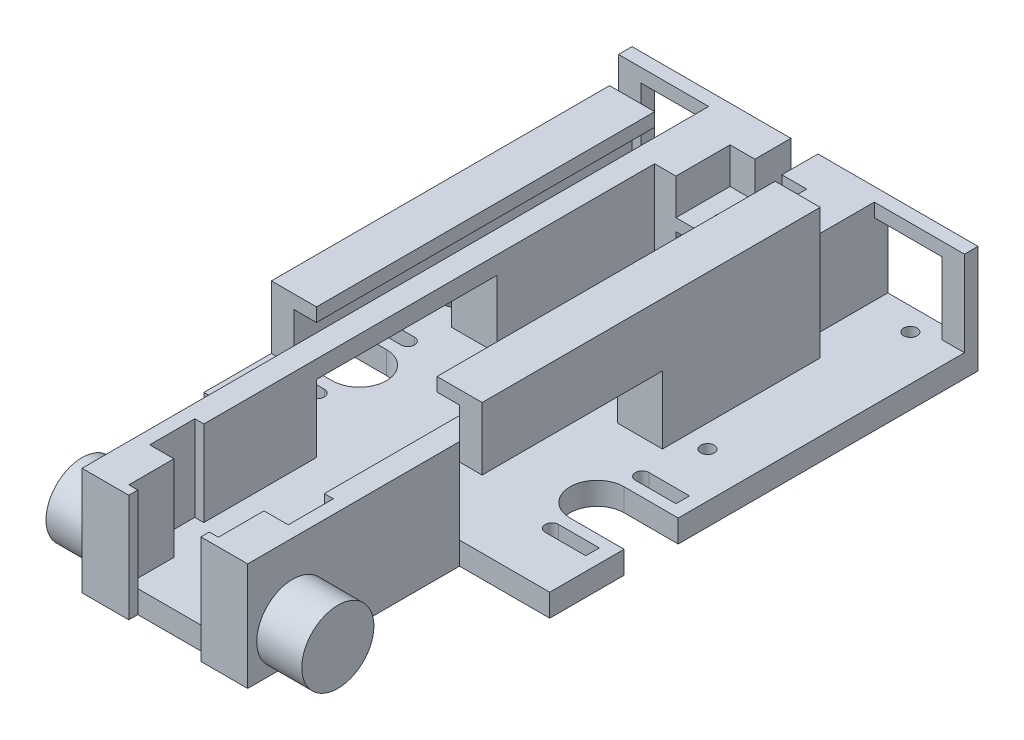
SolidWorks part; units mm, degrees
ref_plane "Front Plane" through (0, 0, 0) normal (0, 0, 1) x (1, 0, 0)
ref_plane "Top Plane" through (0, 0, 0) normal (0, 1, 0) x (1, 0, 0)
ref_plane "Right Plane" through (0, 0, 0) normal (1, 0, 0) x (0, 0, -1)
sketch "Sketch1" plane through (0, 0, 0) normal (0, 0, 1) x (1, 0, 0)
  line L0 (0, 0) -> (33.9598, 0)
  line L1 (33.9598, 0) -> (33.9598, 24.0538)
  line L2 (0, 0) -> (0, 24.0538)
  line L3 (0, 24.0538) -> (-6.35, 24.0538)
  line L4 (33.9598, 24.0538) -> (40.3098, 24.0538)
  line L5 (-6.35, 24.0538) -> (-6.35, -6.35)
  line L6 (40.3098, 24.0538) -> (40.3098, -6.35)
  line L7 (40.3098, -6.35) -> (-6.35, -6.35)
  dimension "D1" = 33.9598
  dimension "D2" = 24.0538
  dimension "D3" = 24.0538
  dimension "D4" = 6.35
  dimension "D5" = 6.35
  dimension "D6" = 8.9803
extrude "Boss-Extrude1" add sketch "Sketch1" against normal blind 203.2
sketch "Sketch3" plane through (-6.35, 0, 0) normal (-1, 0, 0) x (0, 0, 1)
  line L0 (0, 8.8519) -> (-3.81, 8.8519) construction
  line L1 (0, 24.0538) -> (0, -6.35) construction
  line L2 (-3.81, 8.8519) -> (-16.51, 8.8519) construction
  circle A0 centre (-16.51, 8.8519) radius 10.16
  dimension "D3" = 20.32
  dimension "D1" = 3.81
  dimension "D2" = 12.7
sketch "Sketch4" plane through (0, 0, 0) normal (0, 0, 1) x (1, 0, 0)
  line L1 (33.9598, 24.0538) -> (40.3098, 24.0538)
  line L2 (33.9598, 24.0538) -> (33.9598, -6.35)
  line L3 (33.9598, -6.35) -> (40.3098, -6.35)
  line L4 (40.3098, 24.0538) -> (40.3098, -6.35)
  line L5 (-6.35, -6.35) -> (0, -6.35)
  line L6 (-6.35, -6.35) -> (-6.35, 24.0538)
  line L7 (-6.35, 24.0538) -> (0, 24.0538)
  line L8 (0, -6.35) -> (0, 24.0538)
sketch "Sketch8" plane through (0, 0, -203.2) normal (0, 0, -1) x (-1, 0, 0)
  line L1 (-40.3098, -6.35) -> (-33.9598, -6.35)
  line L2 (-40.3098, -6.35) -> (-40.3098, 24.0538)
  line L3 (-40.3098, 24.0538) -> (-33.9598, 24.0538)
  line L4 (-33.9598, -6.35) -> (-33.9598, 24.0538)
  line L5 (6.35, -6.35) -> (0, -6.35)
  line L6 (6.35, -6.35) -> (6.35, 24.0538)
  line L7 (6.35, 24.0538) -> (0, 24.0538)
  line L8 (0, -6.35) -> (0, 24.0538)
extrude "Boss-Extrude9" add sketch "Sketch8" along normal blind 6.35
sketch "Sketch9" plane through (0, 0, 0) normal (1, 0, 0) x (0, 0, -1)
  line L1 (203.2, -6.35) -> (209.55, -6.35)
  line L2 (203.2, -6.35) -> (203.2, 24.0538)
  line L3 (203.2, 24.0538) -> (209.55, 24.0538)
  line L4 (209.55, -6.35) -> (209.55, 24.0538)
extrude "Boss-Extrude10" add sketch "Sketch9" along normal up to next
extrude "Boss-Extrude11" add sketch "Sketch4" along normal blind 6.35
sketch "Sketch10" plane through (33.9598, 0, 0) normal (-1, 0, 0) x (0, 0, 1)
  line L1 (0, -6.35) -> (6.35, -6.35)
  line L2 (0, -6.35) -> (0, 24.0538)
  line L3 (0, 24.0538) -> (6.35, 24.0538)
  line L4 (6.35, -6.35) -> (6.35, 24.0538)
extrude "Boss-Extrude12" add sketch "Sketch10" along normal up to next
sketch "Sketch13" plane through (40.3098, 0, 0) normal (1, 0, 0) x (0, 0, -1)
  line L0 (-6.35, 8.8519) -> (50.8, 8.8519) construction
  line L1 (-6.35, -6.35) -> (-6.35, 24.0538) construction
  line L2 (50.8, -6.35) -> (50.8, 0)
  line L3 (209.55, -6.35) -> (-6.35, -6.35) construction
  line L5 (50.8, 0) -> (101.6, 0)
  line L6 (50.8, 0) -> (50.8, 19.05)
  line L7 (50.8, 19.05) -> (101.6, 19.05)
  line L8 (101.6, 0) -> (101.6, 19.05)
  line L9 (50.8, 0) -> (101.6, 0)
  line L10 (50.8, 0) -> (50.8, -6.35)
  line L11 (50.8, -6.35) -> (101.6, -6.35)
  line L12 (101.6, 0) -> (101.6, -6.35)
  dimension "D1" = 57.15
  dimension "D2" = 6.35
  dimension "D3" = 19.05
  dimension "D4" = 50.8
extrude "Cut-Extrude3" cut sketch "Sketch13" against normal through all contours L5 L8 L7 L6
sketch "Sketch14" plane through (40.3098, 0, 0) normal (1, 0, 0) x (0, 0, -1)
  line L0 (209.55, -6.35) -> (-6.35, -6.35) construction
  line L1 (50.8, 0) -> (95.25, 0)
  line L2 (50.8, 0) -> (50.8, -6.35)
  line L3 (50.8, -6.35) -> (95.25, -6.35)
  line L4 (95.25, 0) -> (95.25, -6.35)
extrude "Boss-Extrude13" add sketch "Sketch14" along normal blind 25.4
sketch "Sketch15" plane through (-6.35, 0, 0) normal (-1, 0, 0) x (0, 0, 1)
  line L0 (-50.8, 0) -> (-50.8, -6.35)
  line L1 (-209.55, -6.35) -> (6.35, -6.35) construction
  line L3 (-101.6, 0) -> (-50.8, 0)
  line L4 (-101.6, 0) -> (-101.6, -6.35)
  line L5 (-101.6, -6.35) -> (-50.8, -6.35)
  line L6 (-50.8, 0) -> (-50.8, -6.35)
  line M2 (-50.8, 0) -> (-101.6, 0)
  line M7 (-209.55, -6.35) -> (6.35, -6.35)
extrude "Boss-Extrude14" add sketch "Sketch15" along normal blind 25.4 contours L4 L0 M2 M7
sketch "Sketch18" plane through (0, 0, 0) normal (0, 1, 0) x (1, 0, 0)
  line L0 (16.9799, 203.2) -> (16.9799, 0) construction
  line L1 (33.9598, 203.2) -> (0, 203.2) construction
  line L2 (33.9598, 0) -> (0, 0) construction
  line L3 (65.7098, 73.025) -> (25.4, 73.025) construction
  line L4 (65.7098, 95.25) -> (65.7098, 50.8) construction
  line L5 (25.4, 73.025) -> (44.45, 73.025)
  circle A0 centre (44.45, 73.025) radius 6.35
  circle A1 centre (-10.4902, 73.025) radius 6.35
  dimension "D1" = 12.7
sketch "Sketch20" plane through (0, 0, -209.55) normal (0, 0, -1) x (-1, 0, 0)
  line L0 (-40.3098, 24.0538) -> (-40.3098, -6.35) construction
  line L1 (6.35, 24.0538) -> (-40.3098, 24.0538)
  line L2 (6.35, 24.0538) -> (6.35, 13.8938)
  line L3 (6.35, 13.8938) -> (-40.3098, 13.8938)
  line L4 (-40.3098, 24.0538) -> (-40.3098, 13.8938)
  dimension "D1" = 10.16
extrude "Cut-Extrude6" cut sketch "Sketch20" against normal blind 6.35
sketch "Sketch28" plane through (0, 0, -95.25) normal (0, 0, -1) x (-1, 0, 0)
  line L1 (-40.3098, 0) -> (-65.7098, 0)
  line L2 (-40.3098, 0) -> (-40.3098, -6.35)
  line L3 (-40.3098, -6.35) -> (-65.7098, -6.35)
  line L4 (-65.7098, 0) -> (-65.7098, -6.35)
extrude "Boss-Extrude16" add sketch "Sketch28" along normal blind 6.35
sketch "Sketch29" plane through (0, 0, 0) normal (0, 1, 0) x (1, 0, 0)
  line L2 (65.7098, 101.6) -> (50.4698, 101.6)
  line L3 (50.4698, 101.6) -> (50.4698, 79.375)
  line L4 (16.9799, 0) -> (16.9799, 203.2) construction
  line L5 (50.4698, 101.6) -> (65.7098, 101.6)
  circle A0 centre (50.4698, 79.375) radius 7.62
  circle A1 centre (-16.51, 79.375) radius 7.62
  dimension "D2" = 15.24
  dimension "D1" = 22.225
extrude "Cut-Extrude7" cut sketch "Sketch29" against normal up to surface (6.35 mm away) up to face at (16.9799, -6.35, -84.6667)
sketch "Sketch30" plane through (0, 0, 0) normal (0, 1, 0) x (1, 0, 0)
  line L0 (50.4698, 86.995) -> (65.7098, 86.995)
  line L1 (65.7098, 101.6) -> (65.7098, 50.8) construction
  line L2 (65.7098, 86.995) -> (65.7098, 71.755)
  line L3 (65.7098, 71.755) -> (50.4698, 71.755)
  line L4 (16.9799, 203.2) -> (16.9799, 0) construction
  line L5 (-31.75, 86.995) -> (-31.75, 71.755)
  line L6 (-31.75, 71.755) -> (-16.51, 71.755)
  line L7 (-16.51, 86.995) -> (-31.75, 86.995)
  circle A0 centre (50.4698, 79.375) radius 7.62 construction
  arc A1 (50.4698, 86.995) -> (50.4698, 71.755) centre (50.4698, 79.375) cw
  arc A2 (-16.51, 86.995) -> (-16.51, 71.755) centre (-16.51, 79.375) ccw
extrude "Cut-Extrude8" cut sketch "Sketch30" against normal blind 6.35
sketch "Sketch32" plane through (40.3098, 0, 0) normal (1, 0, 0) x (0, 0, -1)
  line L0 (-6.35, -6.35) -> (-6.35, 3.81) construction
  line L1 (-6.35, -6.35) -> (-6.35, 24.0538) construction
  line L2 (-6.35, 3.81) -> (3.81, 3.81) construction
  circle A0 centre (3.81, 3.81) radius 10.16
  dimension "D3" = 20.32
  dimension "D1" = 10.16
  dimension "D2" = 10.16
extrude "Boss-Extrude17" add sketch "Sketch32" along normal blind 12.7
sketch "Sketch33" plane through (-6.35, 0, 0) normal (-1, 0, 0) x (0, 0, 1)
  line L0 (6.35, -6.35) -> (6.35, 3.81)
  line L1 (6.35, 24.0538) -> (6.35, -6.35) construction
  line L2 (6.35, 3.81) -> (-3.81, 3.81)
  circle A0 centre (-3.81, 3.81) radius 10.16
  dimension "D1" = 10.16
  dimension "D2" = 10.16
extrude "Boss-Extrude18" add sketch "Sketch33" along normal blind 12.7
sketch "Sketch34" plane through (0, 0, -209.55) normal (0, 0, -1) x (-1, 0, 0)
  line L1 (-40.3098, -6.35) -> (10.9504, -6.35)
  line L2 (-40.3098, -6.35) -> (-40.3098, 38.0137)
  line L3 (-40.3098, 38.0137) -> (10.9504, 38.0137)
  line L4 (10.9504, -6.35) -> (10.9504, 38.0137)
extrude "Cut-Extrude9" cut sketch "Sketch34" against normal blind 63.5
sketch "Sketch35" plane through (0, 0, -146.05) normal (0, 0, -1) x (-1, 0, 0)
  line L1 (-40.3098, -6.35) -> (6.35, -6.35)
  line L2 (-40.3098, -6.35) -> (-40.3098, 24.0538)
  line L3 (-40.3098, 24.0538) -> (6.35, 24.0538)
  line L4 (6.35, -6.35) -> (6.35, 24.0538)
extrude "Boss-Extrude19" add sketch "Sketch35" along normal blind 6.35
sketch "Sketch36" plane through (0, 0, -152.4) normal (0, 0, -1) x (-1, 0, 0)
  line L0 (-40.3098, -6.35) -> (-27.6098, -6.35)
  line L1 (-40.3098, -6.35) -> (6.35, -6.35) construction
  line L2 (-27.6098, -6.35) -> (-27.6098, 0)
  line L3 (6.35, 24.0538) -> (-40.3098, 24.0538) construction
  line L8 (-27.6098, 24.0538) -> (-6.0198, 24.0538)
  line L9 (-27.6098, 24.0538) -> (-27.6098, 13.8938)
  line L10 (-27.6098, 13.8938) -> (-6.0198, 13.8938)
  line L11 (-6.0198, 24.0538) -> (-6.0198, 13.8938)
  dimension "D1" = 10.16
  dimension "D3" = 12.7
  dimension "D4" = 21.59
extrude "Cut-Extrude10" cut sketch "Sketch36" against normal blind 6.35 contours L9 L8 L11 L10
sketch "Sketch37" plane through (0, 0, -101.6) normal (0, 0, -1) x (-1, 0, 0)
  line L1 (-65.7098, 0) -> (-40.3098, 0)
  line L2 (-65.7098, 0) -> (-65.7098, -6.35)
  line L3 (-65.7098, -6.35) -> (-40.3098, -6.35)
  line L4 (-40.3098, 0) -> (-40.3098, -6.35)
  line L5 (6.35, 0) -> (31.75, 0)
  line L6 (6.35, 0) -> (6.35, -6.35)
  line L7 (6.35, -6.35) -> (31.75, -6.35)
  line L8 (31.75, 0) -> (31.75, -6.35)
extrude "Boss-Extrude20" add sketch "Sketch37" along normal blind 12.7
sketch "Sketch38" plane through (0, -6.35, 0) normal (0, -1, 0) x (1, 0, 0)
  line L0 (16.9799, -152.4) -> (16.9799, 6.35) construction
  line L1 (40.3098, -152.4) -> (-6.35, -152.4) construction
  line L2 (-6.35, 6.35) -> (40.3098, 6.35) construction
  line L3 (53.0098, -114.3) -> (53.0098, -107.95) construction
  line L4 (65.7098, -114.3) -> (40.3098, -114.3) construction
  circle A0 centre (53.0098, -107.95) radius 1.905
  circle A1 centre (-19.05, -107.95) radius 1.905
  dimension "D2" = 3.81
  dimension "D1" = 6.35
extrude "Cut-Extrude11" cut sketch "Sketch38" against normal blind 12.7
sketch "Sketch39" plane through (0, 0, 0) normal (0, 1, 0) x (1, 0, 0)
  line L0 (50.4698, 86.995) -> (50.4698, 92.075)
  line L1 (50.4698, 71.755) -> (50.4698, 66.675)
  line L2 (50.4698, 68.58) -> (61.8998, 68.58)
  line L3 (50.4698, 64.77) -> (61.8998, 64.77)
  line L4 (61.8998, 64.77) -> (61.8998, 68.58)
  line L5 (50.4698, 93.98) -> (61.8998, 93.98)
  line L6 (50.4698, 90.17) -> (61.8998, 90.17)
  line L7 (61.8998, 90.17) -> (61.8998, 93.98)
  line L8 (17.4498, 152.4) -> (17.4498, 7.6403) construction
  line L9 (27.6098, 152.4) -> (7.2898, 152.4) construction
  line L10 (-27.0002, 90.17) -> (-27.0002, 93.98)
  line L11 (-15.5702, 90.17) -> (-27.0002, 90.17)
  line L12 (-15.5702, 93.98) -> (-27.0002, 93.98)
  line L13 (-15.5702, 68.58) -> (-27.0002, 68.58)
  line L14 (-27.0002, 64.77) -> (-27.0002, 68.58)
  line L15 (-15.5702, 64.77) -> (-27.0002, 64.77)
  circle A0 centre (50.4698, 92.075) radius 1.905
  circle A1 centre (50.4698, 66.675) radius 1.905
  circle A2 centre (-15.5702, 92.075) radius 1.905
  circle A3 centre (-15.5702, 66.675) radius 1.905
  dimension "D3" = 11.43
  dimension "D1" = 5.08
  dimension "D2" = 5.08
sketch "Sketch44" plane through (0, 13.8938, 0) normal (0, 1, 0) x (1, 0, 0)
  line L0 (16.8148, 146.05) -> (12.0523, 146.05) construction
  line L1 (27.6098, 146.05) -> (6.0198, 146.05) construction
  line L2 (16.8148, 146.05) -> (21.5773, 146.05) construction
  line L3 (21.5773, 152.4) -> (21.5773, 149.225)
  line L4 (27.6098, 152.4) -> (6.0198, 152.4) construction
  line L5 (12.0523, 152.4) -> (12.0523, 149.225)
  circle A0 centre (21.5773, 149.225) radius 1.143
  circle A1 centre (12.0523, 149.225) radius 1.143
  dimension "D4" = 2.286
  dimension "D5" = 2.286
  dimension "D1" = 4.7625
  dimension "D2" = 3.175
  dimension "D3" = 3.175
  dimension "D6" = 9.525
extrude "Cut-Extrude15" cut sketch "Sketch44" against normal through all both and the other way through all
extrude "Cut-Extrude13" cut sketch "Sketch39" against normal blind 8.35
sketch "Sketch40" plane through (0, 24.0538, 0) normal (0, 1, 0) x (1, 0, 0)
  line L0 (16.9799, -6.35) -> (29.6799, -6.35)
  line L1 (40.3098, -6.35) -> (-6.35, -6.35) construction
  line L2 (16.9799, -6.35) -> (4.2799, -6.35)
  line L3 (0, 0) -> (33.9598, 0) construction
  line L4 (4.2799, -6.35) -> (29.6799, -6.35)
  line L5 (4.2799, -6.35) -> (4.2799, 0)
  line L6 (4.2799, 0) -> (29.6799, 0)
  line L7 (29.6799, -6.35) -> (29.6799, 0)
  line M4 (33.9598, 0) -> (0, 0)
  line M7 (-6.35, -6.35) -> (40.3098, -6.35)
extrude "Cut-Extrude14" cut sketch "Sketch40" against normal up to surface (24.0538 mm away) contours L7 L5 M7 M4
sketch "Sketch47" plane through (0, -6.35, 0) normal (0, -1, 0) x (-1, 0, 0)
  line L0 (-16.9799, 152.4) -> (-16.9799, 142.24) construction
  line L1 (-40.3098, 152.4) -> (6.35, 152.4) construction
  circle A0 centre (-16.9799, 142.24) radius 3.556
extrude "Cut-Extrude16" cut sketch "Sketch47" against normal through all
sketch "Sketch48" plane through (0, 13.8938, 0) normal (0, 1, 0) x (1, 0, 0)
  line L0 (21.5773, 148.082) -> (21.5773, 146.05) construction
  line L1 (27.6098, 146.05) -> (6.0198, 146.05) construction
  line L2 (12.0523, 148.082) -> (12.0523, 146.05) construction
  line L3 (21.5773, 146.05) -> (12.0523, 146.05)
  circle A0 centre (21.5773, 149.225) radius 1.143 construction
  circle A1 centre (12.0523, 149.225) radius 1.143 construction
  arc A2 (21.5773, 146.05) -> (12.0523, 146.05) centre (16.8148, 141.2875) ccw
extrude "Cut-Extrude17" cut sketch "Sketch48" against normal up to surface (13.8938 mm away) contours L3 A2 up to face at (16.9799, 0, -138.684)
sketch "Sketch49" plane through (-6.35, 0, 0) normal (-1, 0, 0) x (0, 0, 1)
  line L1 (-152.4, 24.0538) -> (-50.8, 24.0538)
  line L2 (-152.4, 24.0538) -> (-152.4, 19.05)
  line L3 (-152.4, 19.05) -> (-50.8, 19.05)
  line L4 (-50.8, 24.0538) -> (-50.8, 19.05)
extrude "Boss-Extrude23" add sketch "Sketch49" along normal blind 6.35
sketch "Sketch50" plane through (40.3098, 0, 0) normal (1, 0, 0) x (0, 0, -1)
  line L1 (152.4, 24.0538) -> (50.8, 24.0538)
  line L2 (152.4, 24.0538) -> (152.4, 19.05)
  line L3 (152.4, 19.05) -> (50.8, 19.05)
  line L4 (50.8, 24.0538) -> (50.8, 19.05)
extrude "Boss-Extrude24" add sketch "Sketch50" along normal blind 6.35
sketch "Sketch51" plane through (0, 0, 0) normal (0, 1, 0) x (1, 0, 0)
  circle A0 centre (16.9799, 142.24) radius 3.556
  circle A1 centre (16.9799, 142.24) radius 4.7625
extrude "Cut-Extrude18" cut sketch "Sketch51" against normal blind 3.556
sketch "Sketch52" plane through (0, 24.0538, 0) normal (0, 1, 0) x (1, 0, 0)
  line L0 (-12.7, 152.4) -> (6.0198, 152.4) construction
  line L1 (-12.7, 50.8) -> (-6.35, 50.8)
  line L2 (-12.7, 50.8) -> (-12.7, 152.4)
  line L3 (-12.7, 152.4) -> (-6.35, 152.4)
  line L4 (-6.35, 50.8) -> (-6.35, 152.4)
  line L5 (27.6098, 152.4) -> (46.6598, 152.4) construction
  line L6 (46.6598, 50.8) -> (37.1348, 50.8)
  line L7 (46.6598, 50.8) -> (46.6598, 152.4)
  line L8 (46.6598, 152.4) -> (37.1348, 152.4)
  line L9 (37.1348, 50.8) -> (37.1348, 152.4)
extrude "Boss-Extrude25" add sketch "Sketch52" along normal blind 15.24
sketch "Sketch53" plane through (0, 39.2938, 0) normal (0, 1, 0) x (1, 0, 0)
  line L0 (-12.7, 152.4) -> (-12.7, 50.8) construction
  line L1 (46.6598, 50.8) -> (-12.7, 50.8)
  line L2 (46.6598, 50.8) -> (46.6598, 133.35)
  line L3 (46.6598, 133.35) -> (-12.7, 133.35)
  line L4 (-12.7, 50.8) -> (-12.7, 133.35)
  dimension "D1" = 82.55
extrude "Boss-Extrude26" add sketch "Sketch53" along normal blind 3.175
sketch "Sketch54" plane through (0, 0, -152.4) normal (0, 0, -1) x (-1, 0, 0)
  line L1 (12.7, 39.2938) -> (6.35, 39.2938)
  line L2 (12.7, 39.2938) -> (12.7, 19.05)
  line L3 (12.7, 19.05) -> (6.35, 19.05)
  line L4 (6.35, 39.2938) -> (6.35, 19.05)
  line L5 (-40.3098, 19.05) -> (-46.6598, 19.05)
  line L6 (-40.3098, 19.05) -> (-40.3098, 39.2938)
  line L7 (-40.3098, 39.2938) -> (-46.6598, 39.2938)
  line L8 (-46.6598, 19.05) -> (-46.6598, 39.2938)
extrude "Cut-Extrude20" cut sketch "Sketch54" against normal up to surface (19.05 mm away) up to face at (16.4507, 40.3521, -133.35)
sketch "Sketch55" plane through (0, 0, -152.4) normal (0, 0, -1) x (-1, 0, 0)
  line L1 (-40.3098, 39.2938) -> (-37.1348, 39.2938)
  line L2 (-40.3098, 39.2938) -> (-40.3098, 24.0538)
  line L3 (-40.3098, 24.0538) -> (-37.1348, 24.0538)
  line L4 (-37.1348, 39.2938) -> (-37.1348, 24.0538)
extrude "Cut-Extrude21" cut sketch "Sketch55" against normal up to surface (101.6 mm away) up to face at (-3.175, 9.525, -50.8)
sketch "Sketch56" plane through (0, 0, -152.4) normal (0, 0, -1) x (-1, 0, 0)
  line L0 (-16.9799, -6.35) -> (-16.9799, 8.89)
  line L1 (-40.3098, -6.35) -> (6.35, -6.35) construction
  line L2 (-6.0198, 13.8938) -> (-6.0198, 8.89)
  line L3 (-27.6098, 13.8938) -> (-27.6098, 8.89)
  line L5 (-27.6098, 8.89) -> (-6.0198, 8.89)
  line L6 (-27.6098, 8.89) -> (-27.6098, 10.49)
  line L7 (-27.6098, 10.49) -> (-6.0198, 10.49)
  line L8 (-6.0198, 8.89) -> (-6.0198, 10.49)
  dimension "D1" = 1.6
  dimension "D2" = 15.24
extrude "Cut-Extrude23" cut sketch "Sketch56" against normal up to surface (6.35 mm away) contours L7 L3 L5 L2 up to face at (27.7156, 12.6492, -146.05)
sketch "Sketch57" plane through (0, 0, -133.35) normal (0, 0, -1) x (-1, 0, 0)
  line L0 (6.35, 19.05) -> (12.7, 19.05)
  line L1 (12.7, 19.05) -> (12.7, 42.4688)
  line L2 (12.7, 42.4688) -> (-46.6598, 42.4688)
  line L3 (-46.6598, 42.4688) -> (-46.6598, 19.05)
  line L4 (-46.6598, 19.05) -> (-40.3098, 19.05)
  line L5 (-40.3098, 19.05) -> (-40.3098, 39.2938)
  line L6 (-40.3098, 39.2938) -> (6.35, 39.2938)
  line L7 (6.35, 39.2938) -> (6.35, 19.05)
extrude "Cut-Extrude25" cut sketch "Sketch57" against normal up to surface (19.05 mm away) up to face at (-19.05, -3.175, -114.3)
sketch "Sketch58" plane through (0, 0, 6.35) normal (0, 0, 1) x (1, 0, 0)
  line L0 (-6.35, -6.35) -> (40.3098, -6.35) construction
  line L1 (29.6799, 24.0538) -> (32.2199, 24.0538)
  line L2 (29.6799, 24.0538) -> (29.6799, -6.35)
  line L3 (29.6799, -6.35) -> (32.2199, -6.35)
  line L4 (32.2199, 24.0538) -> (32.2199, -6.35)
  line L6 (4.2799, 24.0538) -> (1.7399, 24.0538)
  line L7 (4.2799, 24.0538) -> (4.2799, -6.35)
  line L8 (4.2799, -6.35) -> (1.7399, -6.35)
  line L9 (1.7399, 24.0538) -> (1.7399, -6.35)
  dimension "D1" = 2.54
  dimension "D2" = 2.54
extrude "Boss-Extrude27" add sketch "Sketch58" along normal blind 2.54
sketch "Sketch59" plane through (4.2799, 0, 0) normal (1, 0, 0) x (0, 0, -1)
  line L1 (-8.89, 24.0538) -> (-6.35, 24.0538)
  line L2 (-8.89, 24.0538) -> (-8.89, -6.35)
  line L3 (-8.89, -6.35) -> (-6.35, -6.35)
  line L4 (-6.35, 24.0538) -> (-6.35, -6.35)
extrude "Boss-Extrude28" add sketch "Sketch59" along normal blind 2.54
sketch "Sketch60" plane through (29.6799, 0, 0) normal (-1, 0, 0) x (0, 0, 1)
  line L0 (8.89, -6.35) -> (6.35, -6.35) construction
  line L1 (8.89, 24.0538) -> (6.5199, 24.0538)
  line L2 (8.89, 24.0538) -> (8.89, -6.35)
  line L3 (8.89, -6.35) -> (6.5199, -6.35)
  line L4 (6.5199, 24.0538) -> (6.5199, -6.35)
extrude "Boss-Extrude29" add sketch "Sketch60" along normal blind 2.54
sketch "Sketch61" plane through (1.7399, 0, 0) normal (-1, 0, 0) x (0, 0, 1)
  line L1 (6.35, -6.35) -> (8.89, -6.35)
  line L2 (6.35, -6.35) -> (6.35, 24.0538)
  line L3 (6.35, 24.0538) -> (8.89, 24.0538)
  line L4 (8.89, -6.35) -> (8.89, 24.0538)
extrude "Boss-Extrude30" add sketch "Sketch61" along normal up to surface (8.0899 mm away) up to face at (-6.35, -3.6647, 3.6647)
sketch "Sketch62" plane through (32.2199, 0, 0) normal (1, 0, 0) x (0, 0, -1)
  line L1 (-6.35, 24.0538) -> (-8.89, 24.0538)
  line L2 (-6.35, 24.0538) -> (-6.35, -6.35)
  line L3 (-6.35, -6.35) -> (-8.89, -6.35)
  line L4 (-8.89, 24.0538) -> (-8.89, -6.35)
extrude "Boss-Extrude31" add sketch "Sketch62" along normal up to surface (8.0899 mm away) up to face at (40.3098, 31.6738, -82.55)
sketch "Sketch63" plane through (0, 0, 0) normal (0, 0, -1) x (-1, 0, 0)
  line L1 (0, 0) -> (-4.2799, 0)
  line L2 (0, 0) -> (0, 24.0538)
  line L3 (0, 24.0538) -> (-4.2799, 24.0538)
  line L4 (-4.2799, 0) -> (-4.2799, 24.0538)
  line L5 (-33.9598, 0) -> (-29.6799, 0)
  line L6 (-33.9598, 0) -> (-33.9598, 24.0538)
  line L7 (-33.9598, 24.0538) -> (-29.6799, 24.0538)
  line L8 (-29.6799, 0) -> (-29.6799, 24.0538)
extrude "Boss-Extrude32" add sketch "Sketch63" along normal blind 6.35
sketch "Sketch64" plane through (0, 24.0538, 0) normal (0, 1, 0) x (1, 0, 0)
  line L1 (0, 6.35) -> (-2.54, 6.35)
  line L2 (0, 6.35) -> (0, 19.05)
  line L3 (0, 19.05) -> (-2.54, 19.05)
  line L4 (-2.54, 6.35) -> (-2.54, 19.05)
  line L5 (33.9598, 6.35) -> (36.4998, 6.35)
  line L6 (33.9598, 6.35) -> (33.9598, 19.05)
  line L7 (33.9598, 19.05) -> (36.4998, 19.05)
  line L8 (36.4998, 6.35) -> (36.4998, 19.05)
  dimension "D1" = 2.54
  dimension "D2" = 12.7
  dimension "D3" = 2.54
  dimension "D4" = 12.7
extrude "Cut-Extrude26" cut sketch "Sketch64" against normal up to surface (24.0538 mm away) up to face at (16.9799, 0, -137.4775)
sketch "Sketch65" plane through (0, 0, -152.4) normal (0, 0, -1) x (-1, 0, 0)
  line L0 (6.35, 24.0538) -> (-6.0198, 24.0538)
  line L1 (-6.0198, 24.0538) -> (-6.0198, 13.8938)
  line L2 (-6.0198, 13.8938) -> (-27.6098, 13.8938)
  line L3 (-27.6098, 13.8938) -> (-27.6098, 24.0538)
  line L4 (-27.6098, 24.0538) -> (-40.3098, 24.0538)
  line L5 (-40.3098, 24.0538) -> (-40.3098, -6.35)
  line L6 (-40.3098, -6.35) -> (6.35, -6.35)
  line L7 (6.35, -6.35) -> (6.35, 24.0538)
extrude "Boss-Extrude34" add sketch "Sketch65" along normal blind 19.05
sketch "Sketch66" plane through (0, 42.4688, 0) normal (0, 1, 0) x (1, 0, 0)
  line L1 (46.6598, 50.8) -> (-12.7, 50.8)
  line L2 (46.6598, 50.8) -> (46.6598, 114.3)
  line L3 (46.6598, 114.3) -> (-12.7, 114.3)
  line L4 (-12.7, 50.8) -> (-12.7, 114.3)
extrude "Cut-Extrude27" cut sketch "Sketch66" against normal up to surface (18.415 mm away) up to face at (33.6441, 24.0538, -58.5772)
sketch "Sketch67" plane through (0, 19.05, 0) normal (0, -1, 0) x (1, 0, 0)
  line L1 (40.3098, -101.6) -> (46.6598, -101.6)
  line L2 (40.3098, -101.6) -> (40.3098, -114.3)
  line L3 (40.3098, -114.3) -> (46.6598, -114.3)
  line L4 (46.6598, -101.6) -> (46.6598, -114.3)
extrude "Boss-Extrude35" add sketch "Sketch67" along normal blind 19.05
sketch "Sketch68" plane through (0, 19.05, 0) normal (0, -1, 0) x (1, 0, 0)
  line L1 (-6.35, -101.6) -> (-12.7, -101.6)
  line L2 (-6.35, -101.6) -> (-6.35, -114.3)
  line L3 (-6.35, -114.3) -> (-12.7, -114.3)
  line L4 (-12.7, -101.6) -> (-12.7, -114.3)
extrude "Boss-Extrude36" add sketch "Sketch68" along normal blind 19.05
sketch "Sketch69" plane through (0, 24.0538, 0) normal (0, 1, 0) x (1, 0, 0)
  line L1 (40.3098, 50.8) -> (46.6598, 50.8)
  line L2 (40.3098, 50.8) -> (40.3098, 114.3)
  line L3 (40.3098, 114.3) -> (46.6598, 114.3)
  line L4 (46.6598, 50.8) -> (46.6598, 114.3)
  line L5 (-6.35, 50.8) -> (-12.7, 50.8)
  line L6 (-6.35, 50.8) -> (-6.35, 114.3)
  line L7 (-6.35, 114.3) -> (-12.7, 114.3)
  line L8 (-12.7, 50.8) -> (-12.7, 114.3)
extrude "Boss-Extrude39" add sketch "Sketch69" along normal blind 12.7
sketch "Sketch70" plane through (40.3098, 0, 0) normal (-1, 0, 0) x (0, 0, 1)
  line L0 (-114.3, 36.7538) -> (-114.3, 24.0538) construction
  line L1 (-50.8, 36.7538) -> (-114.3, 36.7538)
  line L2 (-50.8, 36.7538) -> (-50.8, 32.9438)
  line L3 (-50.8, 32.9438) -> (-114.3, 32.9438)
  line L4 (-114.3, 36.7538) -> (-114.3, 32.9438)
  dimension "D1" = 3.81
extrude "Boss-Extrude40" add sketch "Sketch70" along normal up to surface (6.35 mm away) up to face at (33.9598, 10.7759, -79.375)
sketch "Sketch71" plane through (-6.35, 0, 0) normal (1, 0, 0) x (0, 0, -1)
  line L1 (50.8, 36.7538) -> (114.3, 36.7538)
  line L2 (50.8, 36.7538) -> (50.8, 32.9438)
  line L3 (50.8, 32.9438) -> (114.3, 32.9438)
  line L4 (114.3, 36.7538) -> (114.3, 32.9438)
  dimension "D1" = 3.81
extrude "Boss-Extrude41" add sketch "Sketch71" along normal up to surface (6.35 mm away) up to face at (0, 10.7759, -79.375)
sketch "Sketch72" plane through (0, 13.8938, 0) normal (0, 1, 0) x (1, 0, 0)
  line L0 (12.0523, 152.3236) -> (12.0523, 146.05)
  line L1 (21.5773, 146.05) -> (21.5773, 152.3236)
  circle A0 centre (12.0523, 152.3236) radius 1.0865
  circle A1 centre (21.5773, 152.3236) radius 1.143
extrude "Cut-Extrude29" cut sketch "Sketch72" against normal through all
sketch "Sketch73" plane through (0, 13.8938, 0) normal (0, 1, 0) x (1, 0, 0)
  circle A0 centre (12.0523, 149.225) radius 1.143
  circle A1 centre (21.5773, 149.225) radius 1.143
extrude "Boss-Extrude42" add sketch "Sketch73" against normal up to surface (20.2438 mm away) up to face at (12.0523, -6.35, -151.2371)
sketch "Sketch74" plane through (0, 0, -146.05) normal (0, 0, 1) x (1, 0, 0)
  line L1 (6.0198, 10.49) -> (27.6098, 10.49)
  line L2 (6.0198, 10.49) -> (6.0198, 8.89)
  line L3 (6.0198, 8.89) -> (27.6098, 8.89)
  line L4 (27.6098, 10.49) -> (27.6098, 8.89)
extrude "Cut-Extrude30" cut sketch "Sketch74" against normal blind 10.16
sketch "Sketch75" plane through (0, 0, -171.45) normal (0, 0, -1) x (-1, 0, 0)
  line L1 (6.35, 24.0538) -> (-40.3098, 24.0538)
  line L2 (6.35, 24.0538) -> (6.35, -6.35)
  line L3 (6.35, -6.35) -> (-40.3098, -6.35)
  line L4 (-40.3098, 24.0538) -> (-40.3098, -6.35)
extrude "Boss-Extrude43" add sketch "Sketch75" against normal blind 10.16
sketch "Sketch76" plane through (0, 24.0538, 0) normal (0, 1, 0) x (1, 0, 0)
  line L0 (16.8148, 161.29) -> (20.6248, 161.29)
  line L1 (6.0198, 161.29) -> (27.6098, 161.29) construction
  line L2 (20.6248, 161.29) -> (20.6248, 171.45)
  line L3 (-6.35, 171.45) -> (40.3098, 171.45) construction
  line L4 (20.6248, 171.45) -> (13.0048, 171.45)
  line L5 (13.0048, 171.45) -> (13.0048, 161.29)
  line L6 (13.0048, 161.29) -> (16.8148, 161.29)
  dimension "D1" = 3.81
  dimension "D2" = 3.81
extrude "Cut-Extrude32" cut sketch "Sketch76" against normal blind 10.16
sketch "Sketch78" plane through (0, 0, -114.3) normal (0, 0, -1) x (-1, 0, 0)
  line L0 (-40.3098, -6.35) -> (-40.3098, 24.0538) construction
  line L1 (-65.7098, -6.35) -> (-40.3098, -6.35)
  line L2 (-65.7098, -6.35) -> (-65.7098, 0)
  line L3 (-65.7098, 0) -> (-40.3098, 0)
  line L4 (-40.3098, -6.35) -> (-40.3098, 0)
  line L5 (6.35, 24.0538) -> (6.35, -6.35) construction
  line L6 (31.75, -6.35) -> (6.35, -6.35)
  line L7 (31.75, -6.35) -> (31.75, 0)
  line L8 (31.75, 0) -> (6.35, 0)
  line L9 (6.35, -6.35) -> (6.35, 0)
extrude "Boss-Extrude44" add sketch "Sketch78" along normal up to surface (57.15 mm away) up to face at (16.8974, 13.9128, -171.45)
sketch "Sketch79" plane through (0, 0, 0) normal (0, 1, 0) x (1, 0, 0)
  line L0 (53.0098, 107.95) -> (53.0098, 165.1)
  line L1 (40.3098, 171.45) -> (65.7098, 171.45) construction
  line L2 (-19.05, 107.95) -> (-19.05, 165.1)
  line L3 (-31.75, 171.45) -> (-6.35, 171.45) construction
  circle A0 centre (-19.05, 165.1) radius 1.905
  circle A1 centre (53.0098, 165.1) radius 1.905
  dimension "D3" = 3.81
  dimension "D4" = 3.81
  dimension "D1" = 6.35
  dimension "D2" = 6.35
extrude "Cut-Extrude33" cut sketch "Sketch79" against normal through all both and the other way through all
sketch "Sketch80" plane through (65.7098, 0, 0) normal (1, 0, 0) x (0, 0, -1)
  line L0 (171.45, 0) -> (158.75, 0) construction
  line L1 (171.45, 0) -> (86.995, 0) construction
  line L2 (86.995, -6.35) -> (171.45, -6.35) construction
  line L3 (158.75, 0) -> (114.3, 0)
  line L4 (158.75, 0) -> (158.75, -6.35)
  line L5 (158.75, -6.35) -> (114.3, -6.35)
  line L6 (114.3, 0) -> (114.3, -6.35)
  dimension "D1" = 12.7
extrude "Cut-Extrude34" cut sketch "Sketch80" against normal up to surface (25.4 mm away) up to face at (40.3098, 12.0269, -142.875)
sketch "Sketch81" plane through (-31.75, 0, 0) normal (-1, 0, 0) x (0, 0, 1)
  line L0 (-171.45, 0) -> (-158.75, 0) construction
  line L1 (-86.995, 0) -> (-171.45, 0) construction
  line L2 (-171.45, -6.35) -> (-86.995, -6.35) construction
  line L3 (-158.75, 0) -> (-114.3, 0)
  line L4 (-158.75, 0) -> (-158.75, -6.35)
  line L5 (-158.75, -6.35) -> (-114.3, -6.35)
  line L6 (-114.3, 0) -> (-114.3, -6.35)
  dimension "D1" = 44.45
  dimension "D2" = 12.7
extrude "Cut-Extrude35" cut sketch "Sketch81" against normal up to surface (25.4 mm away) up to face at (-6.35, 6.4897, -22.86)
sketch "Sketch82" plane through (0, 0, 0) normal (0, 1, 0) x (1, 0, 0)
  line L1 (-31.75, 171.45) -> (-25.4, 171.45)
  line L2 (-31.75, 171.45) -> (-31.75, 167.64)
  line L3 (-31.75, 167.64) -> (-25.4, 167.64)
  line L4 (-25.4, 171.45) -> (-25.4, 167.64)
  line L6 (65.7098, 171.45) -> (59.3598, 171.45)
  line L7 (65.7098, 171.45) -> (65.7098, 167.64)
  line L8 (65.7098, 167.64) -> (59.3598, 167.64)
  line L9 (59.3598, 171.45) -> (59.3598, 167.64)
  dimension "D1" = 6.35
  dimension "D2" = 6.35
  dimension "D3" = 3.81
  dimension "D4" = 3.81
extrude "Boss-Extrude47" add sketch "Sketch82" along normal up to surface (24.0538 mm away) up to face at (32.0167, 24.0538, -71.4163)
sketch "Sketch83" plane through (59.3598, 0, 0) normal (-1, 0, 0) x (0, 0, 1)
  line L0 (-167.64, 24.0538) -> (-167.64, 0) construction
  line L1 (-171.45, 24.0538) -> (-167.64, 24.0538)
  line L2 (-171.45, 24.0538) -> (-171.45, 20.2438)
  line L3 (-171.45, 20.2438) -> (-167.64, 20.2438)
  line L4 (-167.64, 24.0538) -> (-167.64, 20.2438)
  dimension "D1" = 3.81
extrude "Boss-Extrude48" add sketch "Sketch83" along normal up to surface (19.05 mm away) up to face at (40.3098, 5.9013, -148.1667)
sketch "Sketch84" plane through (-25.4, 0, 0) normal (1, 0, 0) x (0, 0, -1)
  line L0 (171.45, 24.0538) -> (171.45, 0) construction
  line L1 (167.64, 24.0538) -> (171.45, 24.0538)
  line L2 (167.64, 24.0538) -> (167.64, 20.2438)
  line L3 (167.64, 20.2438) -> (171.45, 20.2438)
  line L4 (171.45, 24.0538) -> (171.45, 20.2438)
  dimension "D1" = 3.81
extrude "Boss-Extrude49" add sketch "Sketch84" along normal up to surface (19.05 mm away) up to face at (-6.35, 6.4897, -22.86)
sketch "Sketch85" plane through (0, 0, -114.3) normal (0, 0, -1) x (-1, 0, 0)
  line L1 (6.35, -6.35) -> (31.75, -6.35)
  line L2 (6.35, -6.35) -> (6.35, 0)
  line L3 (6.35, 0) -> (31.75, 0)
  line L4 (31.75, -6.35) -> (31.75, 0)
extrude "Boss-Extrude50" add sketch "Sketch85" along normal up to surface (44.45 mm away) up to face at (-19.05, -3.175, -158.75)
sketch "Sketch86" plane through (0, 0, -114.3) normal (0, 0, -1) x (-1, 0, 0)
  line L1 (-65.7098, 0) -> (-40.3098, 0)
  line L2 (-65.7098, 0) -> (-65.7098, -6.35)
  line L3 (-65.7098, -6.35) -> (-40.3098, -6.35)
  line L4 (-40.3098, 0) -> (-40.3098, -6.35)
extrude "Boss-Extrude51" add sketch "Sketch86" along normal up to surface (44.45 mm away) up to face at (53.0098, -3.175, -158.75)
sketch "Sketch87" plane through (0, 0, -114.3) normal (0, 0, -1) x (-1, 0, 0)
  line L0 (-33.9598, 36.7538) -> (-46.6598, 36.7538)
  line L1 (-46.6598, 36.7538) -> (-46.6598, 0)
  line L2 (-46.6598, 0) -> (-40.3098, 0)
  line L3 (-40.3098, 0) -> (-40.3098, 32.9438)
  line L4 (-40.3098, 32.9438) -> (-33.9598, 32.9438)
  line L5 (-33.9598, 32.9438) -> (-40.3098, 32.9438) construction
  line L6 (-33.9598, 32.9438) -> (-33.9598, 36.7538)
  line L7 (0, 36.7538) -> (12.7, 36.7538)
  line L8 (12.7, 36.7538) -> (12.7, 0)
  line L9 (12.7, 0) -> (6.35, 0)
  line L10 (6.35, 0) -> (6.35, 32.9438)
  line L11 (6.35, 32.9438) -> (0, 32.9438)
  line L12 (0, 32.9438) -> (0, 36.7538)
extrude "Boss-Extrude52" add sketch "Sketch87" along normal up to surface (31.75 mm away) up to face at (7.2288, 11.4655, -146.05)
